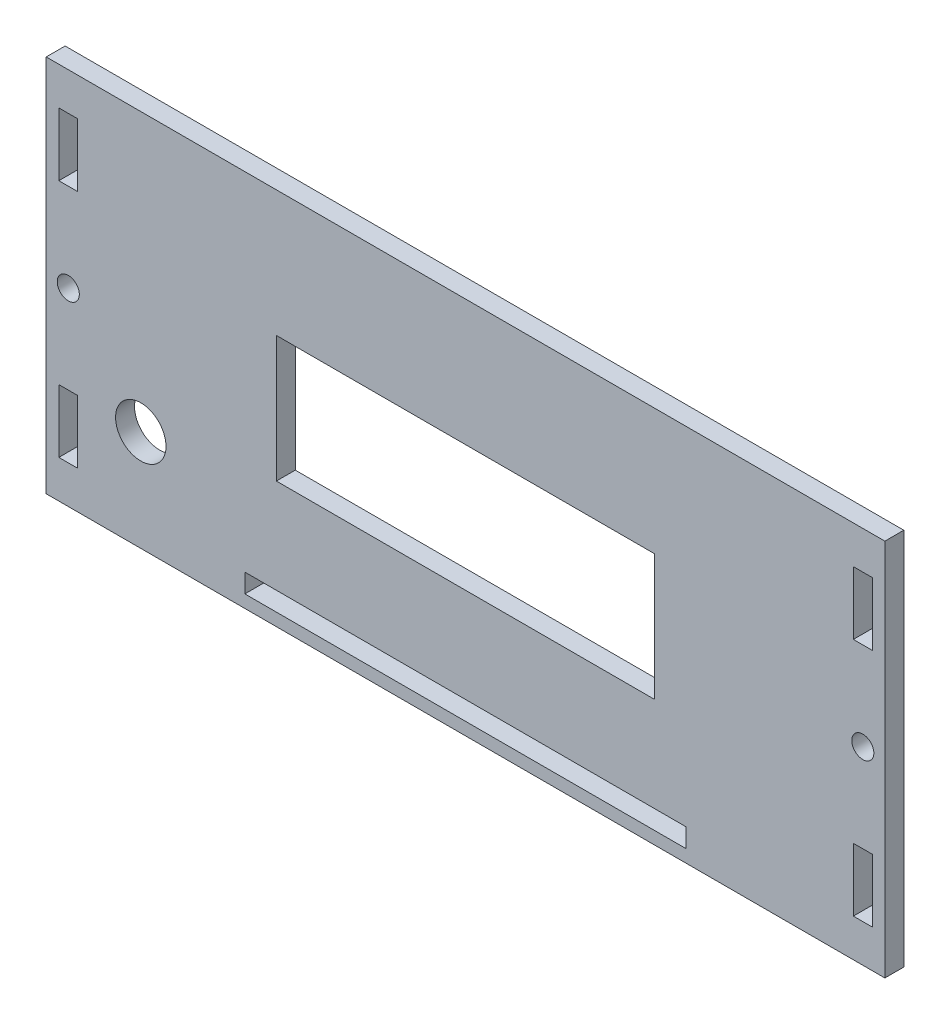
SolidWorks part; units mm, degrees
ref_plane "Front Plane" through (0, 0, 0) normal (0, 0, 1) x (1, 0, 0)
ref_plane "Top Plane" through (0, 0, 0) normal (0, 1, 0) x (1, 0, 0)
ref_plane "Right Plane" through (0, 0, 0) normal (1, 0, 0) x (0, 0, -1)
sketch "Sketch1" plane through (0, 0, 0) normal (0, 0, 1) x (1, 0, 0)
  line L0 (61.5, 24) -> (64.5, 24)
  line L1 (-66.5, 30) -> (66.5, 30)
  line L2 (-66.5, 30) -> (-66.5, -30)
  line L3 (-66.5, -30) -> (66.5, -30)
  line L4 (66.5, 30) -> (66.5, -30)
  line L5 (-66.5, 30) -> (66.5, -30) construction
  line L6 (-66.5, -30) -> (66.5, 30) construction
  line L7 (-30, 10) -> (30, 10)
  line L8 (-30, 10) -> (-30, -10)
  line L9 (-30, -10) -> (30, -10)
  line L10 (30, 10) -> (30, -10)
  line L11 (-30, 10) -> (30, -10) construction
  line L12 (-30, -10) -> (30, 10) construction
  line L13 (-35, -25) -> (35, -25)
  line L14 (-35, -25) -> (-35, -28)
  line L15 (-35, -28) -> (35, -28)
  line L16 (35, -25) -> (35, -28)
  line L17 (-35, -25) -> (35, -28) construction
  line L18 (-35, -28) -> (35, -25) construction
  line L19 (-64.5, 24) -> (-61.5, 24)
  line L20 (-64.5, 24) -> (-64.5, 14)
  line L21 (-64.5, 14) -> (-61.5, 14)
  line L22 (-61.5, 24) -> (-61.5, 14)
  line L23 (-64.5, 24) -> (-61.5, 14) construction
  line L24 (-64.5, 14) -> (-61.5, 24) construction
  line L25 (61.5, 24) -> (61.5, 14)
  line L26 (61.5, 14) -> (64.5, 14)
  line L27 (61.5, 24) -> (64.5, 14) construction
  line L28 (64.5, 24) -> (64.5, 14)
  line L29 (61.5, 14) -> (64.5, 24) construction
  line L30 (-61.5, -14) -> (-61.5, -24)
  line L31 (-64.5, -24) -> (-61.5, -14) construction
  line L32 (-64.5, -14) -> (-61.5, -14)
  line L33 (-64.5, -24) -> (-61.5, -24)
  line L34 (61.5, -14) -> (61.5, -24)
  line L35 (64.5, -14) -> (64.5, -24)
  line L36 (61.5, -14) -> (64.5, -24) construction
  line L37 (61.5, -14) -> (64.5, -14)
  line L38 (61.5, -24) -> (64.5, -24)
  line L39 (-64.5, -14) -> (-64.5, -24)
  line L40 (61.5, -24) -> (64.5, -14) construction
  line L41 (-64.5, -14) -> (-61.5, -24) construction
  circle A0 centre (-51.5, -14) radius 4
  circle A1 centre (-63, 0) radius 1.75
  circle A2 centre (63, 0) radius 1.75
  point P0 (0, 0)
  point P6 (0, 0)
  point P11 (0, -26.5)
  point P17 (-63, 19)
  point P22 (63, 19)
  point P28 (-63, -19)
  point P33 (63, -19)
  dimension "D1" = 133
  dimension "D2" = 60
  dimension "D3" = 60
  dimension "D4" = 20
extrude "Boss-Extrude2" add sketch "Sketch1" along normal blind 3
